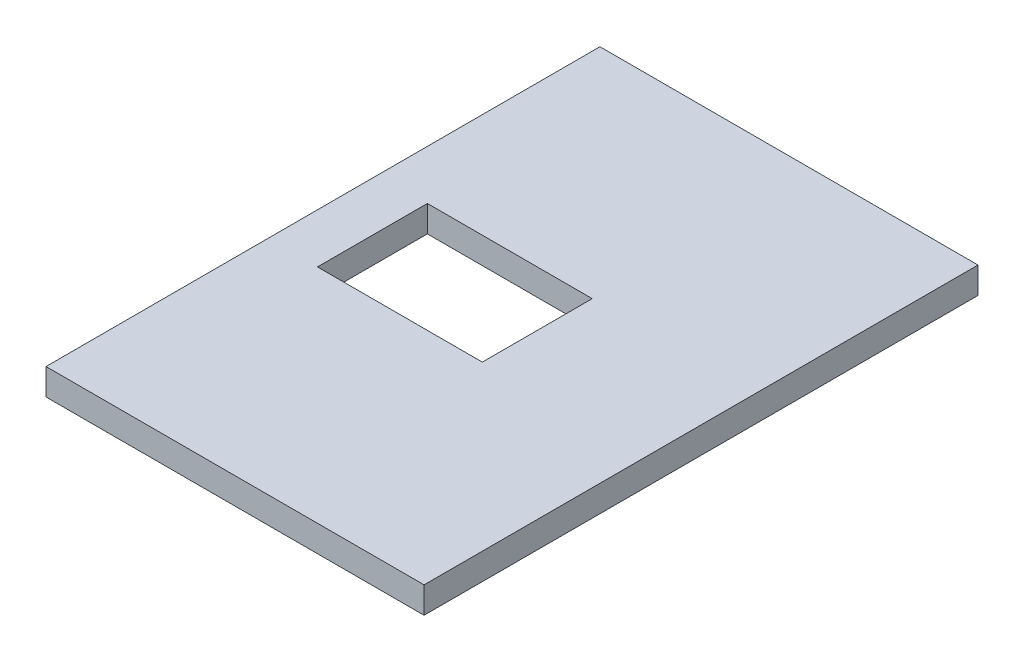
SolidWorks part; units mm, degrees
ref_plane "Alzado" through (0, 0, 0) normal (0, 0, 1) x (1, 0, 0)
ref_plane "Planta" through (0, 0, 0) normal (0, 1, 0) x (1, 0, 0)
ref_plane "Vista lateral" through (0, 0, 0) normal (1, 0, 0) x (0, 0, -1)
sketch "Croquis1" plane through (0, 0, 0) normal (0, 1, 0) x (1, 0, 0)
  line L0 (0, 1188) -> (0, -1188) construction
  line L1 (0, -1188) -> (0, 0) construction
  line L2 (0, 0) -> (738, 0) construction
  line L3 (-710, 1160) -> (710, 1160) construction
  line L4 (-710, 1160) -> (-710, -1160) construction
  line L5 (-710, -1160) -> (710, -1160) construction
  line L6 (710, 1160) -> (710, -1160) construction
  line L7 (-710, 1160) -> (710, -1160) construction
  line L8 (-710, -1160) -> (710, 1160) construction
  line L9 (810, 1260) -> (-810, 1260)
  line L10 (810, 1260) -> (810, -1260)
  line L11 (810, -1260) -> (-810, -1260)
  line L12 (-810, 1260) -> (-810, -1260)
  line L13 (810, 1260) -> (-810, -1260) construction
  line L14 (810, -1260) -> (-810, 1260) construction
  dimension "D1" = 100
  dimension "D2" = 100
extrude "Saliente-Extruir1" add sketch "Croquis1" along normal blind 120
sketch "Croquis2" plane through (0, 120, 0) normal (0, 1, 0) x (1, 0, 0)
  line L0 (-310, 0) -> (-810, 0) construction
  line L1 (-685, -250) -> (65, -250)
  line L2 (-685, -250) -> (-685, 250)
  line L3 (-685, 250) -> (65, 250)
  line L4 (65, -250) -> (65, 250)
  line L5 (65, -250) -> (-310, -250) construction
  line L6 (-310, -250) -> (-310, 250) construction
  line L7 (-810, 1260) -> (-810, -1260) construction
  line L8 (-310, 0) -> (65, 0) construction
  point P0 (0, 0)
  dimension "D1" = 500
  dimension "D2" = 750
  dimension "D3" = 500
extrude "Cortar-Extruir1" cut sketch "Croquis2" against normal blind 120
sketch "Croquis3" plane through (-810, 0, 0) normal (-1, 0, 0) x (0, 0, 1)
  line L0 (-1260, 120) -> (1260, 120)
  line L1 (1260, 120) -> (1260, 0)
  line L2 (1260, 0) -> (-1260, 0)
  line L3 (-1260, 0) -> (-1260, 120)
extrude "Saliente-Extruir2" add sketch "Croquis3" along normal blind 100
